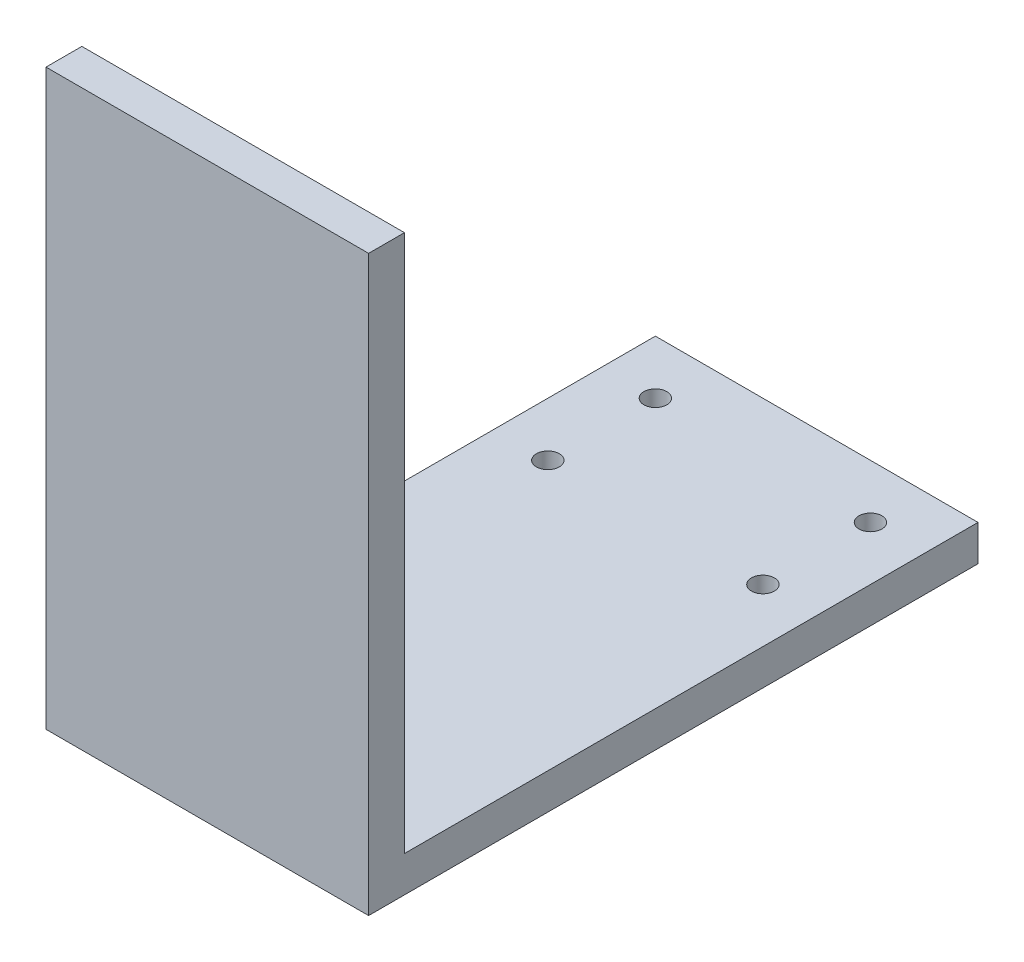
SolidWorks part; units mm, degrees
ref_plane "Front Plane" through (0, 0, 0) normal (0, 0, 1) x (1, 0, 0)
ref_plane "Top Plane" through (0, 0, 0) normal (0, 1, 0) x (1, 0, 0)
ref_plane "Right Plane" through (0, 0, 0) normal (1, 0, 0) x (0, 0, -1)
sketch "Sketch1" plane through (0, 0, 0) normal (0, 1, 0) x (1, 0, 0)
  line L1 (-22.5, -15) -> (22.5, -15)
  line L2 (-22.5, -15) -> (-22.5, 15)
  line L3 (-22.5, 15) -> (22.5, 15)
  line L4 (22.5, -15) -> (22.5, 15)
  line L5 (-22.5, -15) -> (22.5, 15) construction
  line L6 (-22.5, 15) -> (22.5, -15) construction
  point P0 (0, 0)
  dimension "D1" = 30
  dimension "D2" = 45
extrude "Boss-Extrude1" add sketch "Sketch1" along normal blind 5
sketch "Sketch2" plane through (0, 0, 0) normal (0, 1, 0) x (1, 0, 0)
  line L1 (-15, -7.5) -> (15, -7.5) construction
  line L2 (-15, -7.5) -> (-15, 7.5) construction
  line L3 (-15, 7.5) -> (15, 7.5) construction
  line L4 (15, -7.5) -> (15, 7.5) construction
  line L5 (-15, -7.5) -> (15, 7.5) construction
  line L6 (-15, 7.5) -> (15, -7.5) construction
  circle A0 centre (-15, 7.5) radius 1.6
  circle A1 centre (15, 7.5) radius 1.6
  circle A2 centre (15, -7.5) radius 1.6
  circle A3 centre (-15, -7.5) radius 1.6
  point P0 (0, 0)
  dimension "D3" = 3.2
  dimension "D1" = 30
  dimension "D2" = 15
  dimension "D4" = 2
extrude "Cut-Extrude1" cut sketch "Sketch2" along normal up to next
sketch "Sketch4" plane through (0, 0, 15) normal (0, 0, 1) x (1, 0, 0)
  line L1 (-22.5, 5) -> (22.5, 5)
  line L2 (-22.5, 5) -> (-22.5, 0)
  line L3 (-22.5, 0) -> (22.5, 0)
  line L4 (22.5, 5) -> (22.5, 0)
extrude "Boss-Extrude2" add sketch "Sketch4" along normal blind 55
sketch "Sketch5" plane through (0, 5, 0) normal (0, 1, 0) x (1, 0, 0)
  line L0 (-22.5, 15) -> (-22.5, -70) construction
  line L1 (22.5, -70) -> (-22.5, -70)
  line L2 (22.5, -70) -> (22.5, -65)
  line L3 (22.5, -65) -> (-22.5, -65)
  line L4 (-22.5, -70) -> (-22.5, -65)
  dimension "D1" = 5
extrude "Boss-Extrude3" add sketch "Sketch5" along normal blind 75
